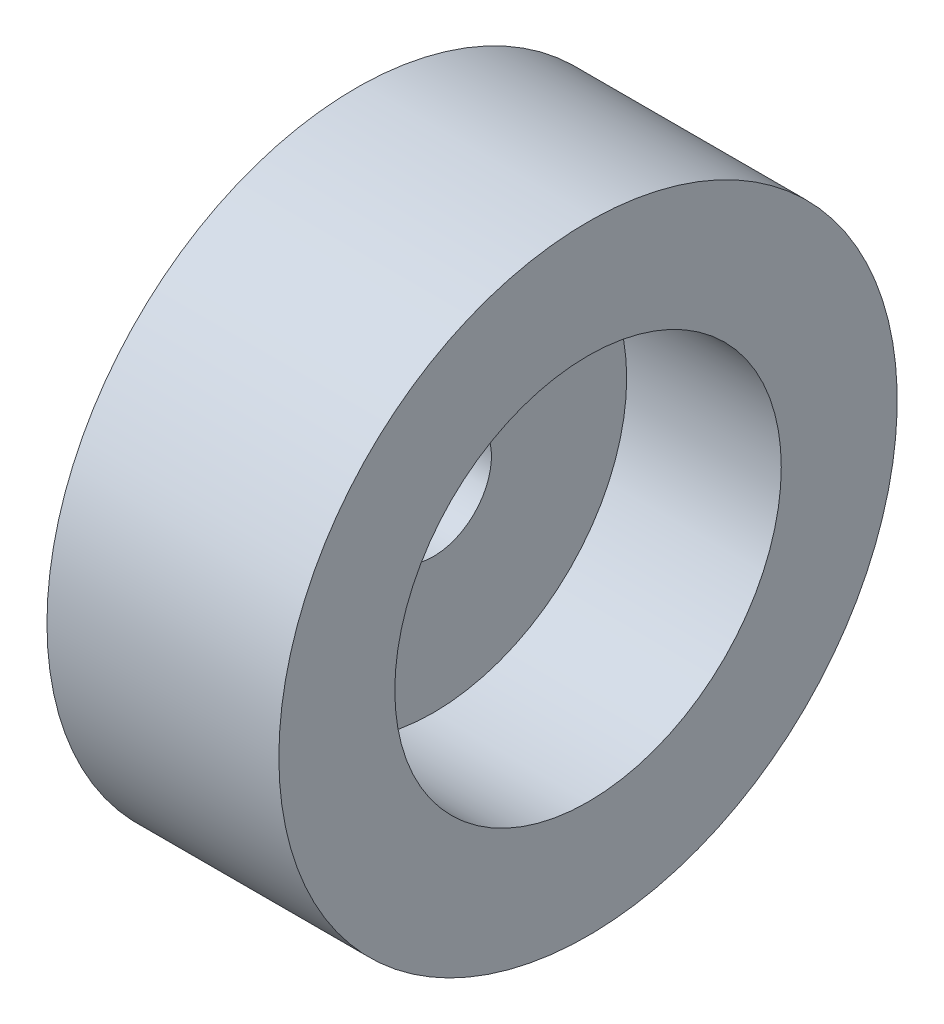
SolidWorks part; units mm, degrees
ref_plane "Front Plane" through (0, 0, 0) normal (0, 0, 1) x (1, 0, 0)
ref_plane "Top Plane" through (0, 0, 0) normal (0, 1, 0) x (1, 0, 0)
ref_plane "Right Plane" through (0, 0, 0) normal (1, 0, 0) x (0, 0, -1)
sketch "Sketch1" plane through (0, 0, 0) normal (0, 0, 1) x (1, 0, 0)
  line L0 (0, 0) -> (7.3225, 0) construction
  line L1 (0, 0.75) -> (2, 0.75)
  line L2 (2, 0.75) -> (2, 2.5)
  line L3 (2, 2.5) -> (4, 2.5)
  line L4 (4, 2.5) -> (4, 4)
  line L5 (4, 4) -> (1, 4)
  line L6 (1, 4) -> (1, 2.5)
  line L7 (1, 2.5) -> (0, 2.5)
  line L8 (0, 2.5) -> (0, 0.75)
  point P5 (0, 0)
  dimension "D1" = 5
  dimension "D2" = 1.5
  dimension "D3" = 5
  dimension "D4" = 8
  dimension "D5" = 3
  dimension "D6" = 2
  dimension "D7" = 1
revolve "Revolve1" add sketch "Sketch1" angle 360 about L0
